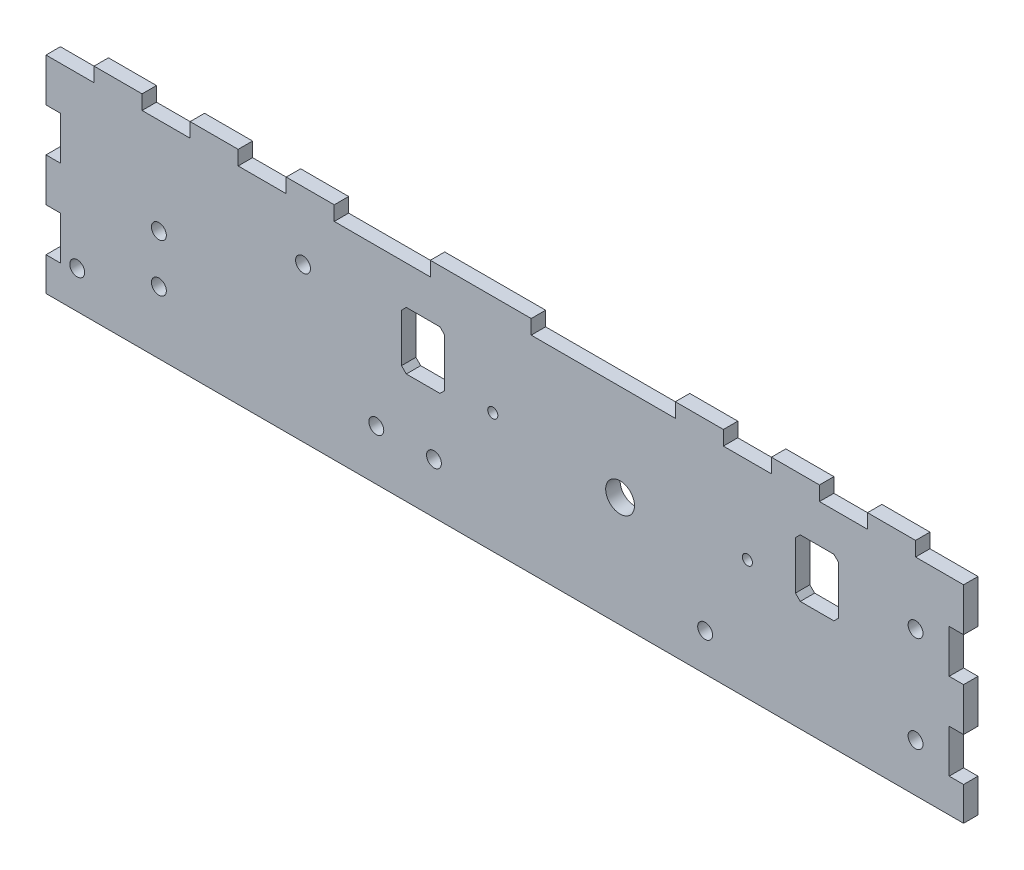
SolidWorks part; units mm, degrees
ref_plane "Front Plane" through (0, 0, 0) normal (0, 0, 1) x (1, 0, 0)
ref_plane "Top Plane" through (0, 0, 0) normal (0, 1, 0) x (1, 0, 0)
ref_plane "Right Plane" through (0, 0, 0) normal (1, 0, 0) x (0, 0, -1)
sketch "Sketch1" plane through (0, 0, 0) normal (0, 0, 1) x (1, 0, 0)
  line L4 (0, 0) -> (191, 0)
  line L5 (191, 0) -> (191, 46)
  line L6 (191, 46) -> (0, 46)
  line L7 (0, 46) -> (0, 0)
  line L8 (0, 0) -> (191, 0)
  line L9 (191, 0) -> (191, 46)
  line L10 (191, 46) -> (0, 46)
  line L11 (0, 46) -> (0, 0)
  circle A0 centre (181, 30) radius 1.55 construction
  circle A1 centre (181, 10) radius 1.55 construction
  circle A2 centre (181, 30) radius 1.55
  circle A3 centre (181, 10) radius 1.55
  dimension "D1" = 0
extrude "Boss-Extrude1" add sketch "Sketch1" along normal blind 3
sketch "Sketch3" plane through (0, 0, 3) normal (0, 0, 1) x (1, 0, 0)
  line L0 (119.5, 46) -> (119.5, 0) construction
  line L1 (119.5, 46) -> (119.5, 0)
  point P2 (119.5, 23)
ref_point "MountPoint-Sus"
sketch "Sketch4" plane through (0, 0, 0) normal (0, 0, -1) x (-1, 0, 0)
  line L0 (-10, 43) -> (-10, 46) construction
  line L1 (-10, 46) -> (0, 46) construction
  line L2 (0, 46) -> (0, 43) construction
  line L3 (0, 43) -> (-10, 43) construction
  line L4 (-30, 43) -> (-30, 46) construction
  line L5 (-30, 46) -> (-20, 46) construction
  line L6 (-20, 46) -> (-20, 43) construction
  line L7 (-20, 43) -> (-30, 43) construction
  line L8 (-50, 43) -> (-50, 46) construction
  line L9 (-50, 46) -> (-40, 46) construction
  line L10 (-40, 46) -> (-40, 43) construction
  line L11 (-40, 43) -> (-50, 43) construction
  line L12 (-60, 43) -> (-80, 43) construction
  line L13 (-80, 43) -> (-80, 46) construction
  line L14 (-80, 46) -> (-60, 46) construction
  line L15 (-60, 46) -> (-60, 43) construction
  line L16 (-131, 43) -> (-131, 46) construction
  line L17 (-131, 46) -> (-101, 46) construction
  line L18 (-101, 46) -> (-101, 43) construction
  line L19 (-101, 43) -> (-131, 43) construction
  line L20 (-151, 43) -> (-151, 46) construction
  line L21 (-151, 46) -> (-141, 46) construction
  line L22 (-141, 46) -> (-141, 43) construction
  line L23 (-141, 43) -> (-151, 43) construction
  line L24 (-171, 43) -> (-171, 46) construction
  line L25 (-171, 46) -> (-161, 46) construction
  line L26 (-161, 46) -> (-161, 43) construction
  line L27 (-161, 43) -> (-171, 43) construction
  line L28 (-191, 46) -> (-181, 46) construction
  line L29 (-181, 46) -> (-181, 43) construction
  line L30 (-181, 43) -> (-191, 43) construction
  line L31 (-191, 43) -> (-191, 46) construction
  line L32 (-10, 43) -> (-10, 46)
  line L33 (-10, 46) -> (0, 46)
  line L34 (0, 46) -> (0, 43)
  line L35 (0, 43) -> (-10, 43)
  line L36 (-30, 43) -> (-30, 46)
  line L37 (-30, 46) -> (-20, 46)
  line L38 (-20, 46) -> (-20, 43)
  line L39 (-20, 43) -> (-30, 43)
  line L40 (-50, 43) -> (-50, 46)
  line L41 (-50, 46) -> (-40, 46)
  line L42 (-40, 46) -> (-40, 43)
  line L43 (-40, 43) -> (-50, 43)
  line L44 (-60, 43) -> (-80, 43)
  line L45 (-80, 43) -> (-80, 46)
  line L46 (-80, 46) -> (-60, 46)
  line L47 (-60, 46) -> (-60, 43)
  line L48 (-131, 43) -> (-131, 46)
  line L49 (-131, 46) -> (-101, 46)
  line L50 (-101, 46) -> (-101, 43)
  line L51 (-101, 43) -> (-131, 43)
  line L52 (-151, 43) -> (-151, 46)
  line L53 (-151, 46) -> (-141, 46)
  line L54 (-141, 46) -> (-141, 43)
  line L55 (-141, 43) -> (-151, 43)
  line L56 (-171, 43) -> (-171, 46)
  line L57 (-171, 46) -> (-161, 46)
  line L58 (-161, 46) -> (-161, 43)
  line L59 (-161, 43) -> (-171, 43)
  line L60 (-191, 46) -> (-181, 46)
  line L61 (-181, 46) -> (-181, 43)
  line L62 (-181, 43) -> (-191, 43)
  line L63 (-191, 43) -> (-191, 46)
extrude "Cut-Extrude1" cut sketch "Sketch4" against normal up to next
sketch "Sketch5" plane through (0, 0, 0) normal (0, 0, -1) x (-1, 0, 0)
  line L4 (0, 34) -> (-3, 34)
  line L5 (0, 25) -> (0, 34)
  line L6 (-3, 25) -> (0, 25)
  line L7 (-3, 34) -> (-3, 25)
  line L8 (0, 34) -> (-3, 34)
  line L9 (0, 25) -> (0, 34)
  line L10 (-3, 25) -> (0, 25)
  line L11 (-3, 34) -> (-3, 25)
  line L12 (-3, 7) -> (0, 7)
  line L13 (0, 7) -> (0, 16)
  line L14 (0, 16) -> (-3, 16)
  line L15 (-3, 16) -> (-3, 7)
  line L16 (-3, 7) -> (0, 7)
  line L17 (0, 7) -> (0, 16)
  line L18 (0, 16) -> (-3, 16)
  line L19 (-3, 16) -> (-3, 7)
  dimension "D1" = 0
  dimension "D2" = 0
extrude "Cut-Extrude2" cut sketch "Sketch5" against normal up to next
sketch "Sketch6" plane through (0, 0, 0) normal (0, 0, -1) x (-1, 0, 0)
  line L0 (-188, 25) -> (-188, 34) construction
  line L1 (-188, 34) -> (-191, 34) construction
  line L2 (-191, 25) -> (-188, 25) construction
  line L3 (-188, 16) -> (-191, 16) construction
  line L4 (-188, 7) -> (-188, 16) construction
  line L5 (-191, 7) -> (-188, 7) construction
  line L6 (-188, 25) -> (-188, 34)
  line L7 (-188, 34) -> (-191, 34)
  line L8 (-191, 25) -> (-188, 25)
  line L9 (-188, 16) -> (-191, 16)
  line L10 (-188, 7) -> (-188, 16)
  line L11 (-191, 7) -> (-188, 7)
  line L40 (-3, 7) -> (-3, 16)
  line L41 (-3, 16) -> (0, 16)
  line L42 (0, 16) -> (0, 25)
  line L43 (0, 25) -> (-3, 25)
  line L44 (-3, 25) -> (-3, 34)
  line L45 (-3, 34) -> (0, 34)
  line L46 (0, 34) -> (0, 43)
  line L47 (0, 43) -> (-10, 43)
  line L48 (-10, 43) -> (-10, 46)
  line L49 (-10, 46) -> (-20, 46)
  line L50 (-20, 46) -> (-20, 43)
  line L51 (-20, 43) -> (-30, 43)
  line L52 (-30, 43) -> (-30, 46)
  line L53 (-30, 46) -> (-40, 46)
  line L54 (-40, 46) -> (-40, 43)
  line L55 (-40, 43) -> (-50, 43)
  line L56 (-50, 43) -> (-50, 46)
  line L57 (-50, 46) -> (-60, 46)
  line L58 (-60, 46) -> (-60, 43)
  line L59 (-60, 43) -> (-80, 43)
  line L60 (-80, 43) -> (-80, 46)
  line L61 (-80, 46) -> (-101, 46)
  line L62 (-101, 46) -> (-101, 43)
  line L63 (-101, 43) -> (-131, 43)
  line L64 (-131, 43) -> (-131, 46)
  line L65 (-131, 46) -> (-141, 46)
  line L66 (-141, 46) -> (-141, 43)
  line L67 (-141, 43) -> (-151, 43)
  line L68 (-151, 43) -> (-151, 46)
  line L69 (-151, 46) -> (-161, 46)
  line L70 (-161, 46) -> (-161, 43)
  line L71 (-161, 43) -> (-171, 43)
  line L72 (-171, 43) -> (-171, 46)
  line L73 (-171, 46) -> (-181, 46)
  line L74 (-181, 46) -> (-181, 43)
  line L75 (-181, 43) -> (-191, 43)
  line L76 (-191, 43) -> (-191, 0)
  line L77 (-191, 0) -> (0, 0)
  line L78 (0, 0) -> (0, 7)
  line L79 (0, 7) -> (-3, 7)
  line L80 (-3, 7) -> (-3, 16)
  line L81 (-3, 16) -> (0, 16)
  line L82 (0, 16) -> (0, 25)
  line L83 (0, 25) -> (-3, 25)
  line L84 (-3, 25) -> (-3, 34)
  line L85 (-3, 34) -> (0, 34)
  line L86 (0, 34) -> (0, 43)
  line L87 (0, 43) -> (-10, 43)
  line L88 (-10, 43) -> (-10, 46)
  line L89 (-10, 46) -> (-20, 46)
  line L90 (-20, 46) -> (-20, 43)
  line L91 (-20, 43) -> (-30, 43)
  line L92 (-30, 43) -> (-30, 46)
  line L93 (-30, 46) -> (-40, 46)
  line L94 (-40, 46) -> (-40, 43)
  line L95 (-40, 43) -> (-50, 43)
  line L96 (-50, 43) -> (-50, 46)
  line L97 (-50, 46) -> (-60, 46)
  line L98 (-60, 46) -> (-60, 43)
  line L99 (-60, 43) -> (-80, 43)
  line L100 (-80, 43) -> (-80, 46)
  line L101 (-80, 46) -> (-101, 46)
  line L102 (-101, 46) -> (-101, 43)
  line L103 (-101, 43) -> (-131, 43)
  line L104 (-131, 43) -> (-131, 46)
  line L105 (-131, 46) -> (-141, 46)
  line L106 (-141, 46) -> (-141, 43)
  line L107 (-141, 43) -> (-151, 43)
  line L108 (-151, 43) -> (-151, 46)
  line L109 (-151, 46) -> (-161, 46)
  line L110 (-161, 46) -> (-161, 43)
  line L111 (-161, 43) -> (-171, 43)
  line L112 (-171, 43) -> (-171, 46)
  line L113 (-171, 46) -> (-181, 46)
  line L114 (-181, 46) -> (-181, 43)
  line L115 (-181, 43) -> (-191, 43)
  line L116 (-191, 43) -> (-191, 0)
  line L117 (-191, 0) -> (0, 0)
  line L118 (0, 0) -> (0, 7)
  line L119 (0, 7) -> (-3, 7)
  line M78 (-191, 43) -> (-191, 0)
  dimension "D1" = 0
extrude "Cut-Extrude3" cut sketch "Sketch6" against normal up to next contours L8 L6 L7 M78 | L11 L10 L9 M78
sketch "Sketch7" plane through (0, 0, 3) normal (0, 0, 1) x (1, 0, 0)
  circle A0 centre (119.5, 23) radius 3
  point P0 (119.5, 23)
  dimension "D1" = 6
extrude "Cut-Extrude4" cut sketch "Sketch7" against normal up to next
sketch "Sketch8" plane through (0, 0, 3) normal (0, 0, 1) x (1, 0, 0)
  circle A0 centre (23.5, 13) radius 1.55 construction
  circle A1 centre (23.5, 23) radius 1.55 construction
  circle A2 centre (53.5, 32) radius 1.55 construction
  circle A3 centre (68.7574, 10.5) radius 1.55 construction
  circle A4 centre (80.7574, 10.5) radius 1.55 construction
  circle A5 centre (23.5, 13) radius 1.55
  circle A6 centre (23.5, 23) radius 1.55
  circle A7 centre (53.5, 32) radius 1.55
  circle A8 centre (68.7574, 10.5) radius 1.55
  circle A9 centre (80.7574, 10.5) radius 1.55
extrude "Cut-Extrude5" cut sketch "Sketch8" against normal up to next
sketch "Sketch9" plane through (0, 0, 0) normal (0, 0, -1) x (-1, 0, 0)
  circle A0 centre (-137.2, 7.8) radius 1.55 construction
  circle A1 centre (-6.5, 7.8) radius 1.55 construction
  circle A2 centre (-137.2, 7.8) radius 1.55
  circle A3 centre (-6.5, 7.8) radius 1.55
extrude "Cut-Extrude6" cut sketch "Sketch9" against normal up to next
sketch "Sketch10" plane through (0, 0, 3) normal (0, 0, 1) x (1, 0, 0)
  line L14 (83, 24) -> (83, 34) construction
  line L15 (82, 35) -> (83, 34) construction
  line L16 (82, 35) -> (75, 35) construction
  line L17 (74, 34) -> (75, 35) construction
  line L18 (74, 34) -> (74, 24) construction
  line L19 (75, 23) -> (74, 24) construction
  line L20 (75, 23) -> (82, 23) construction
  line L21 (83, 24) -> (82, 23) construction
  line L22 (83, 24) -> (83, 34)
  line L23 (82, 35) -> (83, 34)
  line L24 (82, 35) -> (75, 35)
  line L25 (74, 34) -> (75, 35)
  line L26 (74, 34) -> (74, 24)
  line L27 (75, 23) -> (74, 24)
  line L28 (75, 23) -> (82, 23)
  line L29 (83, 24) -> (82, 23)
  circle A0 centre (93, 25) radius 1.05 construction
  circle A1 centre (93, 25) radius 1.05
extrude "Cut-Extrude7" cut sketch "Sketch10" against normal up to next
sketch "Sketch11" plane through (0, 0, 3) normal (0, 0, 1) x (1, 0, 0)
  line L0 (119.5, 23) -> (119.5, 33.077) construction
  line L1 (75, 23) -> (82, 23) construction
  line L2 (74, 24) -> (75, 23) construction
  line L3 (74, 34) -> (74, 24) construction
  line L4 (75, 35) -> (74, 34) construction
  line L5 (82, 35) -> (75, 35) construction
  line L6 (83, 34) -> (82, 35) construction
  line L7 (83, 24) -> (83, 34) construction
  line L8 (82, 23) -> (83, 24) construction
  line L9 (75, 23) -> (82, 23)
  line L10 (74, 24) -> (75, 23)
  line L11 (74, 34) -> (74, 24)
  line L12 (75, 35) -> (74, 34)
  line L13 (82, 35) -> (75, 35)
  line L14 (83, 34) -> (82, 35)
  line L15 (83, 24) -> (83, 34)
  line L16 (82, 23) -> (83, 24)
  line L17 (157, 23) -> (156, 24)
  line L18 (156, 24) -> (156, 34)
  line L19 (156, 34) -> (157, 35)
  line L20 (157, 35) -> (164, 35)
  line L21 (164, 35) -> (165, 34)
  line L22 (165, 34) -> (165, 24)
  line L23 (165, 24) -> (164, 23)
  line L24 (164, 23) -> (157, 23)
  circle A0 centre (93, 25) radius 1.05 construction
  circle A1 centre (93, 25) radius 1.05
  circle A2 centre (146, 25) radius 1.05
extrude "Cut-Extrude8" cut sketch "Sketch11" against normal up to next contours L24 L23 L22 L21 L20 L19 L18 L17 | A2
